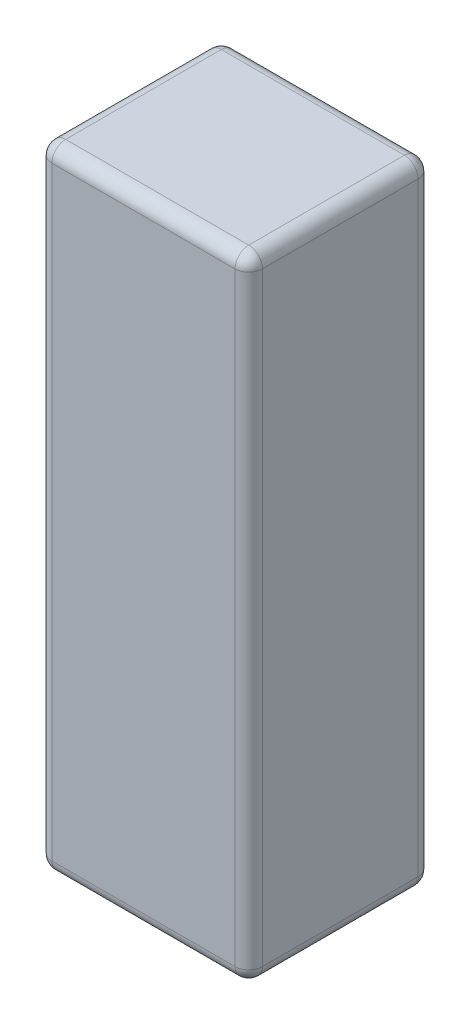
SolidWorks part; units mm, degrees
ref_plane "Front Plane" through (0, 0, 0) normal (0, 0, 1) x (1, 0, 0)
ref_plane "Top Plane" through (0, 0, 0) normal (0, 1, 0) x (1, 0, 0)
ref_plane "Right Plane" through (0, 0, 0) normal (1, 0, 0) x (0, 0, -1)
sketch "Sketch1" plane through (0, 0, 0) normal (0, 1, 0) x (1, 0, 0)
  line L1 (-23, -20) -> (23, -20)
  line L2 (-23, -20) -> (-23, 20)
  line L3 (-23, 20) -> (23, 20)
  line L4 (23, -20) -> (23, 20)
  line L5 (-23, -20) -> (23, 20) construction
  line L6 (-23, 20) -> (23, -20) construction
  point P0 (0, 0)
  point P5 (0, 0)
  dimension "D1" = 40
  dimension "D2" = 46
extrude "Boss-Extrude1" add sketch "Sketch1" along normal blind 138
fillet "Fillet1" radius 3 12 edges at (23, 0, 0) (0, 0, -20) (-23, 0, 0) (0, 0, 20) (23, 138, 0) (0, 138, -20) (-23, 138, 0) (0, 138, 20) (23, 69, 20) (-23, 69, 20) (-23, 69, -20) (23, 69, -20)
